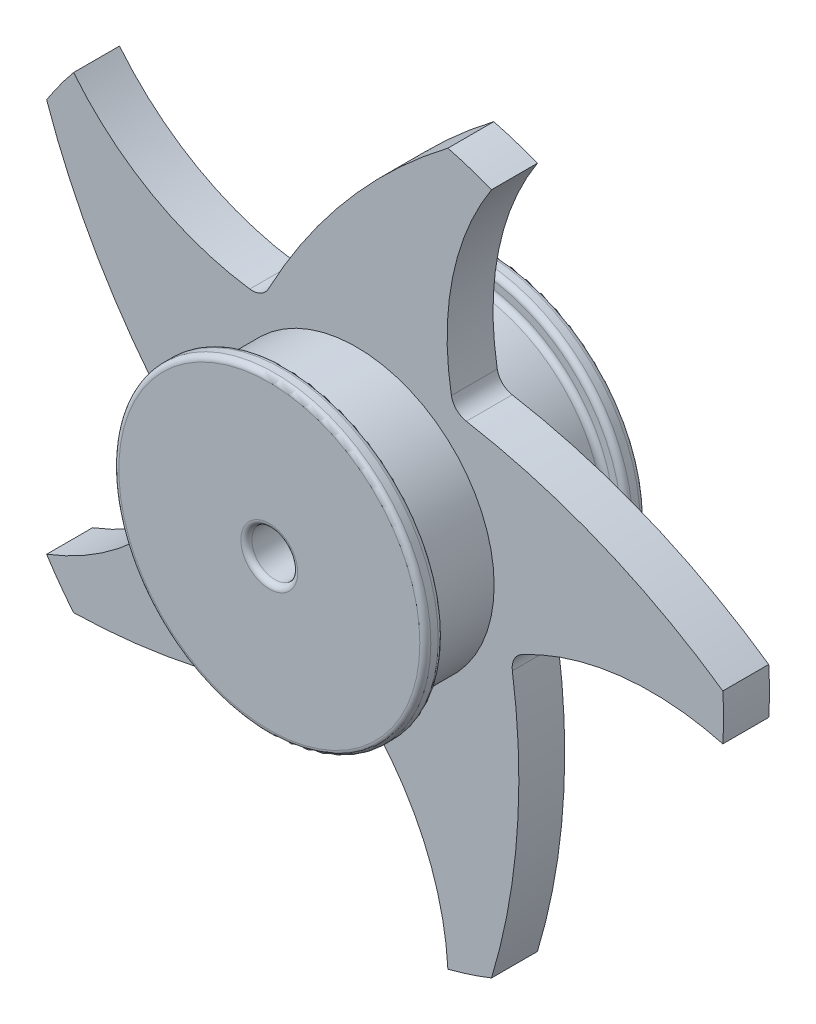
SolidWorks part; units mm, degrees
ref_plane "Front Plane" through (0, 0, 0) normal (0, 0, 1) x (1, 0, 0)
ref_plane "Top Plane" through (0, 0, 0) normal (0, 1, 0) x (1, 0, 0)
ref_plane "Right Plane" through (0, 0, 0) normal (1, 0, 0) x (0, 0, -1)
sketch "Sketch1" plane through (0, 0, 0) normal (0, 0, 1) x (1, 0, 0)
  circle A0 centre (0, 0) radius 75
  circle A1 centre (0, 0) radius 12.5
  dimension "D1" = 150
  dimension "D2" = 25
extrude "Boss-Extrude1" add sketch "Sketch1" along normal mid plane 120
sketch "Sketch2" plane through (0, 0, 60) normal (0, 0, 1) x (1, 0, 0)
  circle A0 centre (0, 0) radius 85
  circle A1 centre (0, 0) radius 75
  circle A2 centre (0, 0) radius 75
  dimension "D1" = 0
  dimension "D2" = 10
extrude "Boss-Extrude2" add sketch "Sketch2" against normal blind 10
fillet "Fillet1" radius 3 5 edges at (75, 0, 50) (85, 0, 50) (85, 0, 60) (12.5, 0, -60) (12.5, 0, 60)
mirror "Mirror2" about plane through (0, 0, 0) normal (0, 0, 1) of "Boss-Extrude2", "Fillet1"
sketch "Sketch3" plane through (0, 0, 0) normal (0, 0, 1) x (1, 0, 0)
  line L0 (0, 0) -> (0, 50000) construction
  line L1 (0, 0) -> (50000, 0) construction
  arc A0 (199.609, -12.5) -> (199.609, 12.5) centre (0, 0) ccw
  arc A1 (0, 75) -> (199.609, 12.5) centre (0, -275) cw
  arc A2 (53.5967, -52.4633) -> (199.609, -12.5) centre (160.79, -157.3899) cw
  circle A4 centre (0, 0) radius 75
  arc A5 (53.5967, -52.4633) -> (0, 75) centre (0, 0) ccw
  point P1 (53.5967, -52.4633)
  dimension "D1" = 400
  dimension "D2" = 350
  dimension "D4" = 150
  dimension "D5" = 25
  dimension "D3" = 0
extrude "Boss-Extrude3" add sketch "Sketch3" along normal mid plane 25
pattern_circular "CirPattern1" count 5 over 360 about axis through (0, 0, 0) along (0, 0, 1) of "Boss-Extrude3"
fillet "Fillet2" radius 10 5 edges at (-84.6797, -26.169, 0) (-51.0556, 72.4485, 0) (-1.2793, -88.6218, 0) (83.889, -28.6023, 0) (53.1256, 70.9446, 0)
